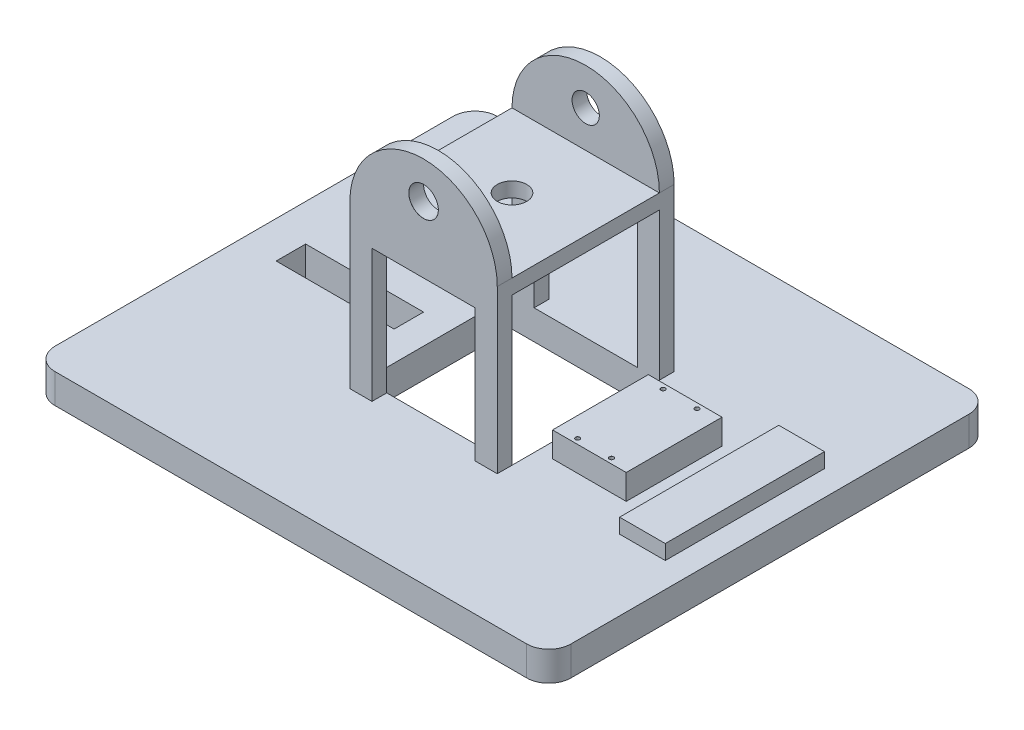
SolidWorks part; units mm, degrees
ref_plane "Front Plane" through (0, 0, 0) normal (0, 0, 1) x (1, 0, 0)
ref_plane "Top Plane" through (0, 0, 0) normal (0, 1, 0) x (1, 0, 0)
ref_plane "Right Plane" through (0, 0, 0) normal (1, 0, 0) x (0, 0, -1)
sketch "Sketch1" plane through (0, 0, 0) normal (0, 1, 0) x (1, 0, 0)
  line L1 (0, 0) -> (350, 0)
  line L2 (0, 0) -> (0, -300)
  line L3 (0, -300) -> (350, -300)
  line L4 (350, 0) -> (350, -300)
  dimension "D1" = 350
  dimension "D2" = 300
extrude "Boss-Extrude1" add sketch "Sketch1" along normal blind 20
fillet "Fillet1" radius 15 4 edges at (350, 10, 0) (0, 10, 0) (0, 10, 300) (350, 10, 300)
sketch "Sketch2" plane through (0, 20, 0) normal (0, 1, 0) x (1, 0, 0)
  line L0 (335, 0) -> (15, 0) construction
  line L1 (125, -100) -> (225, -100)
  line L2 (125, -100) -> (125, -200)
  line L3 (125, -200) -> (225, -200)
  line L4 (225, -100) -> (225, -200)
  line L8 (175, -100) -> (175, 0) construction
  line L9 (175, -200) -> (175, -300) construction
  line L10 (15, -300) -> (335, -300) construction
  line L11 (125, -150) -> (0, -150) construction
  line L12 (0, -15) -> (0, -285) construction
  line L13 (225, -150) -> (350, -150) construction
  line L14 (350, -285) -> (350, -15) construction
  dimension "D2" = 100
  dimension "D1" = 100
extrude "Cut-Extrude1" cut sketch "Sketch2" against normal blind 20 contours L1 L4 L3 L2
sketch "Sketch6" plane through (0, 0, 100) normal (0, 0, 1) x (1, 0, 0)
  line L0 (125, 0) -> (125, 130)
  line L1 (225, 130) -> (225, 0)
  line L2 (15, 0) -> (335, 0) construction
  line L3 (125, 130) -> (225, 130) construction
  line L4 (125, 0) -> (225, 0)
  arc A0 (125, 130) -> (225, 130) centre (175, 130) cw
  dimension "D1" = 100
  dimension "D2" = 130
extrude "Boss-Extrude2" add sketch "Sketch6" against normal blind 10
pattern_linear "LPattern1" count 2 spacing 110 along (0, 0, 1) of "Boss-Extrude2"
sketch "Sketch23" plane through (0, 0, 210) normal (0, 0, 1) x (1, 0, 0)
  line L0 (125, 130) -> (225, 130) construction
  line L1 (225, 130) -> (175, 130) construction
  line L2 (175, 130) -> (175, 180) construction
  line L3 (175, 180) -> (175, 155) construction
  line L4 (175, 155) -> (218.3013, 155) construction
  arc A0 (225, 130) -> (125, 130) centre (175, 130) ccw construction
hole_wizard "Ø20.0 (20) Diameter Hole2" positions "Sketch24" profile "Sketch25" hole size "Ø20.0" standard "ANSI Metric"
sketch "Sketch24" plane through (0, 0, 210) normal (0, 0, 1) x (1, 0, 0)
  point P0 (175, 155)
sketch "Sketch25" plane through (175, 155, 210) normal (1, 0, 0) x (0, -1, 0)
  line L0 (0, 0) -> (0, 16.0086)
  line L1 (0, 16.0086) -> (10, 10)
  line L2 (10, 10) -> (10, 0.025)
  line L3 (10, 0.025) -> (10.025, 0)
  line L5 (10.025, 0) -> (0, 0)
  line L6 (-10, 0.025) -> (-10.025, 0) construction
  line L10 (0, 16.0086) -> (-10, 10) construction
  line L11 (0, -6.35) -> (0, 107.95) construction
  dimension "Hole Dia." = 20
  dimension "Hole Depth" = 10
  dimension "Near C'Sink Dia." = 20.05
  dimension "Near C'Sink Angle" = 90
  dimension "Drill Angle" = 118
hole_wizard "Ø18.5 (18.5) Diameter Hole1" positions "Sketch29" profile "Sketch30" hole size "Ø18.5" standard "ANSI Metric"
sketch "Sketch29" plane through (0, 0, 90) normal (0, 0, -1) x (-1, 0, 0)
  point P0 (-175, 155)
sketch "Sketch30" plane through (175, 155, 90) normal (1, 0, 0) x (0, 1, 0)
  line L0 (0, 0) -> (0, 15.558)
  line L1 (0, 15.558) -> (9.25, 10)
  line L2 (9.25, 10) -> (9.25, 0.025)
  line L3 (9.25, 0.025) -> (9.275, 0)
  line L5 (9.275, 0) -> (0, 0)
  line L6 (-9.25, 0.025) -> (-9.275, 0) construction
  line L10 (0, 15.558) -> (-9.25, 10) construction
  line L11 (0, -6.35) -> (0, 107.95) construction
  dimension "Hole Dia." = 18.5
  dimension "Hole Depth" = 10
  dimension "Near C'Sink Dia." = 18.55
  dimension "Near C'Sink Angle" = 90
  dimension "Drill Angle" = 118
sketch "Sketch32" plane through (0, 0, 210) normal (0, 0, 1) x (1, 0, 0)
  line L0 (125, 130) -> (125, 20) construction
  line L16 (125, 130) -> (225, 130)
  line L17 (125, 130) -> (125, 120)
  line L18 (125, 120) -> (225, 120)
  line L19 (225, 130) -> (225, 120)
  line L20 (225, 20) -> (225, 130) construction
  line L21 (225, 20) -> (125, 20) construction
  dimension "D1" = 100
  dimension "D2" = 10
extrude "Boss-Extrude3" add sketch "Sketch32" against normal blind 120
sketch "Sketch37" plane through (0, 130, 0) normal (0, 1, 0) x (1, 0, 0)
  line L0 (175, -90) -> (175, -210) construction
  line L1 (225, -90) -> (125, -90) construction
  line L2 (125, -210) -> (225, -210) construction
  line L3 (175, -210) -> (175, -150) construction
  line L4 (175, -150) -> (225, -150) construction
  line L5 (225, -100) -> (225, -200) construction
  line L6 (225, -150) -> (125, -150) construction
  line L7 (125, -100) -> (125, -200) construction
  circle A0 centre (175, -150) radius 10
  dimension "D1" = 20
extrude "Cut-Extrude2" cut sketch "Sketch37" against normal blind 36.0783
sketch "Sketch45" plane through (0, 20, 0) normal (0, 1, 0) x (1, 0, 0)
  line L0 (260, -117.5) -> (260, 0) construction
  line L1 (245, -117.5) -> (275, -117.5)
  line L2 (245, -117.5) -> (245, -182.5)
  line L3 (245, -182.5) -> (275, -182.5)
  line L4 (275, -117.5) -> (275, -182.5)
  line L5 (335, 0) -> (15, 0) construction
  line L6 (260, -182.5) -> (260, -300) construction
  line L7 (15, -300) -> (335, -300) construction
  line L8 (350, -285) -> (350, -15) construction
  line L12 (275, -117.5) -> (285, -117.5)
  line L13 (275, -117.5) -> (275, -182.5)
  line L14 (275, -182.5) -> (285, -182.5)
  line L15 (285, -117.5) -> (285, -182.5)
  line L16 (245, -117.5) -> (235, -117.5)
  line L17 (245, -117.5) -> (245, -182.5)
  line L18 (245, -182.5) -> (235, -182.5)
  line L19 (235, -117.5) -> (235, -182.5)
  dimension "D1" = 65
  dimension "D2" = 30
  dimension "D3" = 75
  dimension "D4" = 10
extrude "Boss-Extrude4" add sketch "Sketch45" along normal blind 17 contours L4 L3 L2 L1
hole_wizard "M2.5 Clearance Hole1" positions "Sketch50" profile "Sketch51" hole size "M2.5" standard "ISO"
sketch "Sketch50" plane through (0, 37, 0) normal (0, 1, 0) x (1, 0, 0)
  line L0 (245, -117.5) -> (275, -117.5) construction
  line L1 (245, -117.5) -> (245, -182.5) construction
  line L2 (245, -117.5) -> (275, -117.5) construction
  line L3 (275, -117.5) -> (275, -182.5) construction
  line L4 (245, -182.5) -> (275, -182.5) construction
  point P0 (248.5, -121)
  point P2 (271.5, -121)
  point P3 (271.5, -179)
  point P5 (248.5, -179)
  dimension "D1" = 3.5
  dimension "D2" = 3.5
  dimension "D3" = 3.5
  dimension "D4" = 3.5
  dimension "D5" = 3.5
  dimension "D6" = 3.5
  dimension "D7" = 3.5
  dimension "D8" = 3.5
sketch "Sketch51" plane through (248.5, 37, 121) normal (1, 0, 0) x (0, 0, 1)
  line L0 (0, 0) -> (0, 13.2712)
  line L1 (0, 13.2712) -> (1.45, 12.4)
  line L2 (1.45, 12.4) -> (1.45, 0.025)
  line L3 (1.45, 0.025) -> (1.475, 0)
  line L5 (1.475, 0) -> (0, 0)
  line L6 (-1.45, 0.025) -> (-1.475, 0) construction
  line L10 (0, 13.2712) -> (-1.45, 12.4) construction
  line L11 (0, -6.35) -> (0, 107.95) construction
  dimension "Hole Dia." = 2.9
  dimension "Hole Depth" = 12.4
  dimension "Near C'Sink Dia." = 2.95
  dimension "Near C'Sink Angle" = 90
  dimension "Drill Angle" = 118
sketch "Sketch54" plane through (0, 20, 0) normal (0, 1, 0) x (1, 0, 0)
  line L1 (275, -117.5) -> (285, -117.5)
  line L2 (275, -117.5) -> (275, -182.5)
  line L3 (275, -182.5) -> (285, -182.5)
  line L4 (285, -117.5) -> (285, -182.5)
  line L5 (245, -117.5) -> (235, -117.5)
  line L6 (245, -117.5) -> (245, -182.5)
  line L7 (245, -182.5) -> (235, -182.5)
  line L8 (235, -117.5) -> (235, -182.5)
  dimension "D1" = 10
extrude "Boss-Extrude5" add sketch "Sketch54" along normal blind 17
sketch "Sketch55" plane through (0, 20, 0) normal (0, 1, 0) x (1, 0, 0)
  line L0 (317.5, -96) -> (317.5, 0) construction
  line L1 (302, -96) -> (333, -96)
  line L2 (302, -96) -> (302, -204)
  line L3 (302, -204) -> (333, -204)
  line L4 (333, -96) -> (333, -204)
  line L5 (335, 0) -> (15, 0) construction
  line L6 (317.5, -204) -> (317.5, -300) construction
  line L7 (15, -300) -> (335, -300) construction
  line L8 (333, -150) -> (350, -150) construction
  line L9 (350, -285) -> (350, -15) construction
  line L10 (302, -150) -> (285, -150) construction
  line L12 (285, -182.5) -> (285, -117.5) construction
  dimension "D1" = 108
  dimension "D2" = 31
extrude "Boss-Extrude6" add sketch "Sketch55" along normal blind 10
sketch "Sketch59" plane through (0, 20, 0) normal (0, 1, 0) x (1, 0, 0)
  line L0 (65, -140) -> (65, 0) construction
  line L1 (25, -140) -> (105, -140)
  line L2 (25, -140) -> (25, -160)
  line L3 (25, -160) -> (105, -160)
  line L4 (105, -140) -> (105, -160)
  line L5 (335, 0) -> (15, 0) construction
  line L6 (65, -160) -> (65, -300) construction
  line L7 (15, -300) -> (335, -300) construction
  line L8 (0, -15) -> (0, -285) construction
  dimension "D1" = 20
  dimension "D2" = 80
  dimension "D3" = 25
extrude "Cut-Extrude3" cut sketch "Sketch59" against normal through all contours L1 L4 L3 L2
sketch "Sketch60" plane through (0, 0, 210) normal (0, 0, 1) x (1, 0, 0)
  line L0 (175, 110) -> (175, 130) construction
  line L1 (140, 110) -> (210, 110)
  line L2 (140, 110) -> (140, 20)
  line L3 (140, 20) -> (210, 20)
  line L4 (210, 110) -> (210, 20)
  line L5 (125, 130) -> (225, 130) construction
  line L6 (225, 20) -> (125, 20) construction
  line L8 (210, 65) -> (225, 65) construction
  line L9 (225, 20) -> (225, 130) construction
  line L10 (140, 65) -> (125, 65) construction
  line L11 (125, 130) -> (125, 20) construction
  dimension "D1" = 20
  dimension "D2" = 15
extrude "Cut-Extrude4" cut sketch "Sketch60" against normal blind 180
sketch "Sketch64" plane through (0, 0, 0) normal (0, 0, -1) x (-1, 0, 0)
  line L0 (-305, -15) -> (-305, 0)
  line L1 (-335, 0) -> (-15, 0) construction
  line L2 (-305, 0) -> (-279, 0)
  line L3 (-279, 0) -> (-279, -15)
  line L4 (-335, 20) -> (-335, 0) construction
  line L5 (-175, -33.7864) -> (-175, 53.7864) construction
  line L6 (-175, 10) -> (-335, 10) construction
  line L7 (-175, 10) -> (-15, 10) construction
  line L8 (-15, 0) -> (-15, 20) construction
  line L9 (-71, 0) -> (-71, -15)
  line L10 (-45, 0) -> (-71, 0)
  line L11 (-45, -15) -> (-45, 0)
  line L12 (-305, -15) -> (-305, 0)
  line L13 (-305, 0) -> (-279, 0)
  line L14 (-279, 0) -> (-279, -15)
  line L15 (-71, 0) -> (-71, -15)
  line L16 (-45, 0) -> (-71, 0)
  line L17 (-45, -15) -> (-45, 0)
  circle A0 centre (-292, -15) radius 13
  circle A1 centre (-292, -15) radius 11
  circle A2 centre (-292, -15) radius 3.65
  circle A3 centre (-58, -15) radius 3.65
  circle A4 centre (-58, -15) radius 11
  circle A5 centre (-58, -15) radius 13
  circle A6 centre (-292, -15) radius 13
  circle A7 centre (-292, -15) radius 11
  circle A8 centre (-292, -15) radius 3.65
  circle A9 centre (-58, -15) radius 3.65
  circle A10 centre (-58, -15) radius 11
  circle A11 centre (-58, -15) radius 13
  line M3 (-335, 0) -> (-15, 0)
  dimension "D1" = 26
  dimension "D2" = 22
  dimension "D4" = 15
  dimension "D5" = 7.3
  dimension "D3" = 30
extrude "Boss-Extrude7" add sketch "Sketch64" against normal blind 10 contours A0 L3 L0 M3 | A0 A1 | A1
sketch "Sketch70" plane through (0, 0, 0) normal (0, 0, -1) x (-1, 0, 0)
  circle A0 centre (-292, -15) radius 11
  dimension "D1" = 22
extrude "Cut-Extrude5" cut sketch "Sketch70" against normal blind 7
sketch "Sketch75" plane through (0, 0, 0) normal (0, 0, -1) x (-1, 0, 0)
  line L0 (-71, -15) -> (-71, 0)
  line L1 (-71, 0) -> (-45, 0)
  line L2 (-45, 0) -> (-45, -15)
  line L3 (-279, 0) -> (-15, 0) construction
  line L4 (-71, -15) -> (-71, 0)
  line L5 (-71, 0) -> (-45, 0)
  line L6 (-45, 0) -> (-45, -15)
  line L7 (-15, 0) -> (-15, 20) construction
  circle A0 centre (-58, -15) radius 13
  circle A1 centre (-58, -15) radius 11
  circle A2 centre (-58, -15) radius 3.65
  circle A3 centre (-58, -15) radius 13
  circle A4 centre (-58, -15) radius 11
  circle A5 centre (-58, -15) radius 3.65
  line M9 (-279, 0) -> (-15, 0)
  dimension "D1" = 26
  dimension "D2" = 22
  dimension "D4" = 7.3
  dimension "D3" = 15
  dimension "D5" = 30
extrude "Boss-Extrude8" add sketch "Sketch75" against normal blind 8 contours A0 A1 | A1 A2 | A0 L2 L0 M9
sketch "Sketch77" plane through (0, 0, 0) normal (0, 0, -1) x (-1, 0, 0)
  circle A0 centre (-58, -15) radius 11
  circle A1 centre (-58, -15) radius 3.65 construction
  dimension "D1" = 22
extrude "Cut-Extrude6" cut sketch "Sketch77" against normal blind 7 contours A0
ref_plane "Plane1" through (45, -15, 0) normal (0, 1, 0) x (1, 0, 0)
equation "\"bar_width\"=100"
equation "\"D2@Sketch2\"=\"bar_width\""
equation "\"bar_length\"=100"
equation "\"D1@Sketch2\"=\"bar_length\""
equation "\"D1@Boss-Extrude3\"=\"bar_length\" + 20mm"
equation "\"tower-height\"=100"
equation "\"D1@Sketch32\"=\"tower-height\""
equation "\"lens_diameter\"=20"
equation "\"D1@Sketch37\"=\"lens_diameter\""
equation "\"R_pi_length\"=65"
equation "\"D1@Sketch45\"=\"R_pi_length\""
equation "\"R_pi_width\"=30"
equation "\"D2@Sketch45\"=\"R_pi_width\""
equation "\"RP_tappings\"=3.5"
equation "\"D1@Sketch50\"=\"RP_tappings\""
equation "\"R_pi_height\"=10"
equation "\"Single_battery_width\"= 31mm"
equation "\"D2@Sketch55\"=\"Single_battery_width\""
